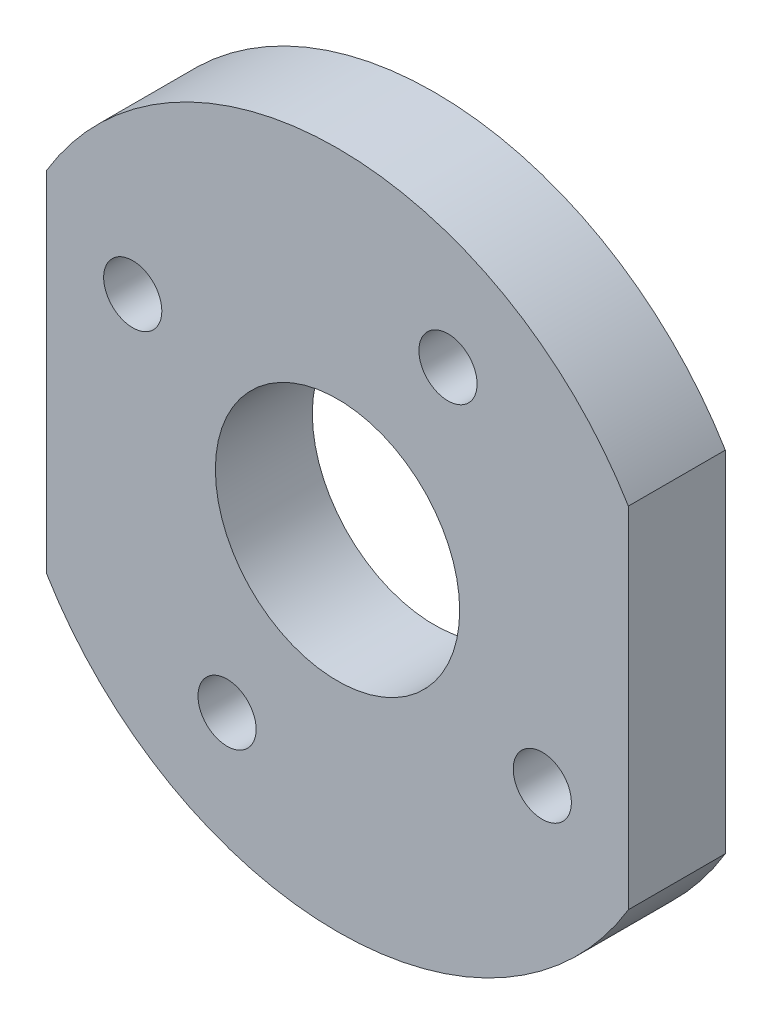
SolidWorks part; units mm, degrees
ref_plane "Front Plane" through (0, 0, 0) normal (0, 0, 1) x (1, 0, 0)
ref_plane "Top Plane" through (0, 0, 0) normal (0, 1, 0) x (1, 0, 0)
ref_plane "Right Plane" through (0, 0, 0) normal (1, 0, 0) x (0, 0, -1)
sketch "Sketch2" plane through (0, 0, 0) normal (0, 0, 1) x (1, 0, 0)
  line L0 (-3.6549, 65.0365) -> (-3.6549, 47.0087)
  line L5 (26.3451, 65.0365) -> (26.3451, 47.0087)
  circle A0 centre (11.3451, 56.0226) radius 6.3
  arc A1 (-3.6549, 47.0087) -> (26.3451, 47.0087) centre (11.3451, 56.0226) ccw
  circle A2 centre (17.0424, 66.5839) radius 1.5
  circle A3 centre (5.6478, 45.4613) radius 1.5
  circle A4 centre (0.7838, 61.7199) radius 1.5
  circle A5 centre (21.9064, 50.3253) radius 1.5
  arc A9 (26.3451, 65.0365) -> (-3.6549, 65.0365) centre (11.3451, 56.0226) ccw
  dimension "D1" = 12.6
  dimension "D2" = 35
  dimension "D3" = 3
  dimension "D4" = 3
  dimension "D5" = 3
  dimension "D6" = 3
  dimension "D7" = 30
  dimension "D8" = 15
extrude "Boss-Extrude1" add sketch "Sketch2" along normal blind 5
sketch "Sketch Wire Slot" plane through (0, 0, 0) normal (0, 0, -1) x (-1, 0, 0)
  line L0 (-1.5421, 51.5242) -> (-0.6823, 54.3984) construction
  line L1 (-2.9792, 51.9541) -> (-2.1193, 54.8283)
  line L2 (-0.105, 51.0943) -> (0.7548, 53.9685)
  line L3 (-0.7838, 61.7199) -> (-0.6823, 54.3984) construction
  line L4 (-5.6478, 45.4613) -> (-1.5421, 51.5242) construction
  circle A0 centre (-5.6478, 45.4613) radius 1.5 construction
  circle A1 centre (-0.7838, 61.7199) radius 1.5 construction
  circle A2 centre (-5.6478, 45.4613) radius 1.5 construction
  circle A3 centre (-0.7838, 61.7199) radius 1.5 construction
  circle A4 centre (-11.3451, 56.0226) radius 6.3 construction
  circle A5 centre (-11.3451, 56.0226) radius 6.3 construction
  arc A6 (-0.7838, 61.7199) -> (-5.6478, 45.4613) centre (-17.3808, 57.8283) cw construction
  arc A7 (-2.9792, 51.9541) -> (-0.105, 51.0943) centre (-1.5421, 51.5242) ccw
  arc A8 (0.7548, 53.9685) -> (-2.1193, 54.8283) centre (-0.6823, 54.3984) ccw
  point P10 (-1.1122, 52.9613)
  dimension "D1" = 3
  dimension "D2" = 3
extrude "Cut-Extrude Wire Slot" [suppressed] cut sketch "Sketch Wire Slot" against normal through all
